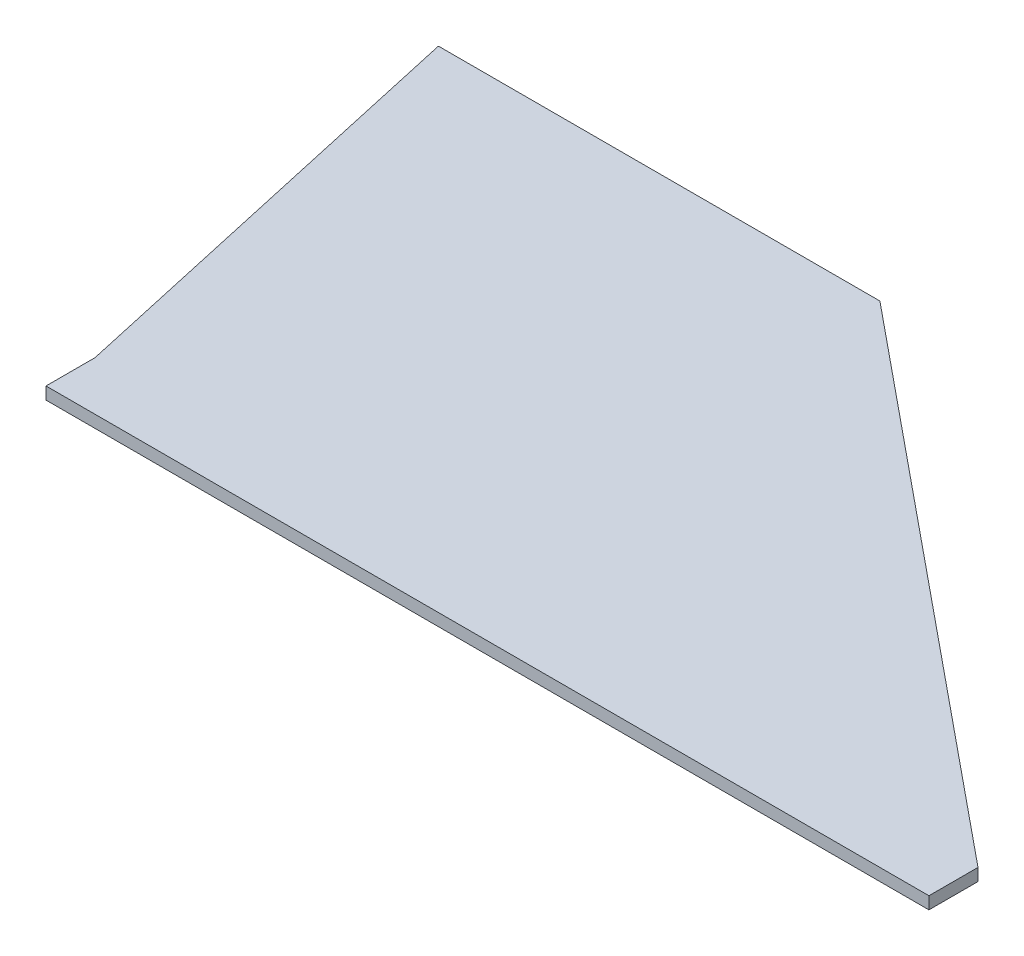
SolidWorks part; units mm, degrees
ref_plane "Front Plane" through (0, 0, 0) normal (0, 0, 1) x (1, 0, 0)
ref_plane "Top Plane" through (0, 0, 0) normal (0, 1, 0) x (1, 0, 0)
ref_plane "Right Plane" through (0, 0, 0) normal (1, 0, 0) x (0, 0, -1)
sketch "Sketch1" plane through (0, 0, 0) normal (0, 1, 0) x (1, 0, 0)
  line L0 (0, 25.4) -> (-50.8, 254)
  line L1 (0, 0) -> (457.2, 0)
  line L2 (0, 0) -> (0, 25.4)
  line L4 (457.2, 0) -> (457.2, 25.4)
  line L5 (-50.8, 254) -> (177.8, 254)
  line L6 (177.8, 254) -> (457.2, 25.4)
  dimension "D1" = 457.2
  dimension "D2" = 25.4
  dimension "D3" = 50.8
  dimension "D4" = 228.6
  dimension "D5" = 228.6
  dimension "D6" = 457.2
extrude "Boss-Extrude1" add sketch "Sketch1" along normal blind 6.35
